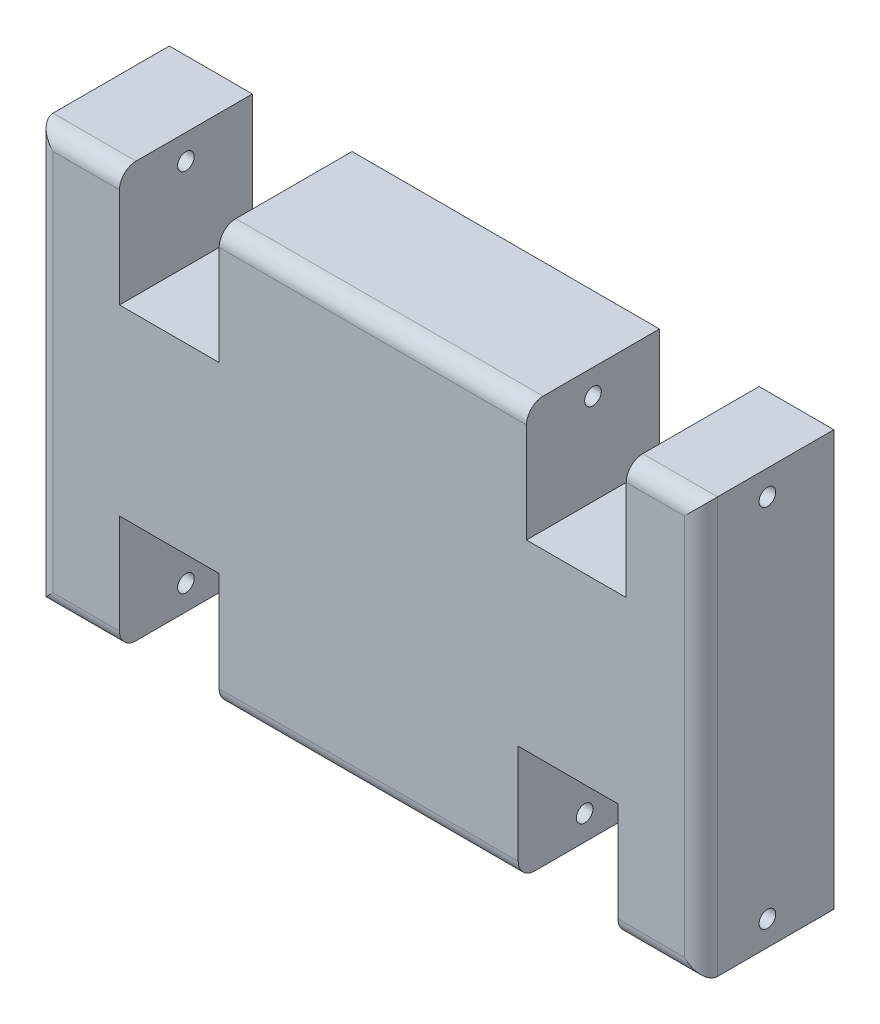
SolidWorks part; units mm, degrees
ref_plane "Alzado" through (0, 0, 0) normal (0, 0, 1) x (1, 0, 0)
ref_plane "Planta" through (0, 0, 0) normal (0, 1, 0) x (1, 0, 0)
ref_plane "Vista lateral" through (0, 0, 0) normal (1, 0, 0) x (0, 0, -1)
sketch "Croquis1" plane through (0, 0, 0) normal (0, 0, 1) x (1, 0, 0)
  line L0 (0, 0) -> (5, 0)
  line L1 (5, 0) -> (5, 7)
  line L2 (5, 7) -> (11, 7)
  line L3 (11, 7) -> (11, 0)
  line L4 (11, 0) -> (29, 0)
  line L5 (29, 7) -> (35, 7)
  line L6 (35, 7) -> (35, 0)
  line L7 (35, 0) -> (40, 0)
  line L8 (29, 7) -> (29, 0)
  line L10 (29.5, 18) -> (29.5, 25)
  line L11 (35.5, 25) -> (40, 25)
  line L12 (35.5, 18) -> (35.5, 25)
  line L13 (29.5, 18) -> (35.5, 18)
  line L14 (11, 25) -> (29.5, 25)
  line L15 (11, 18) -> (11, 25)
  line L16 (5, 18) -> (11, 18)
  line L17 (5, 25) -> (5, 18)
  line L18 (0, 25) -> (5, 25)
  line L19 (0, 25) -> (0, 0)
  line L20 (40, 25) -> (40, 0)
  dimension "D1" = 6
  dimension "D2" = 5
  dimension "D3" = 18
  dimension "D4" = 6
  dimension "D5" = 5
  dimension "D6" = 25
  dimension "D7" = 7
  dimension "D8" = 7
  dimension "D9" = 25
  dimension "D10" = 7
  dimension "D11" = 25
  dimension "D12" = 6
  dimension "D13" = 6
extrude "Saliente-Extruir2" add sketch "Croquis1" along normal blind 8
sketch "Croquis3" plane through (40, 0, 0) normal (1, 0, 0) x (0, 0, -1)
  circle A0 centre (-4, 23.4982) radius 0.5
  circle A1 centre (-4, 1.5018) radius 0.5
  dimension "D1" = 1
extrude "Cortar-Extruir1" cut sketch "Croquis3" against normal blind 45 contours A1 | A0
fillet "Redondeo1" radius 1 1 edges at (20, 0, 8)
fillet "Redondeo2" radius 1 3 edges at (37.5, 0, 8) (40, 12.5, 8) (37.75, 25, 8)
fillet "Redondeo3" radius 1 1 edges at (20.25, 25, 8)
fillet "Redondeo4" radius 1 3 edges at (0, 12.5, 8) (2.5, 25, 8) (2.5, 0, 8)
